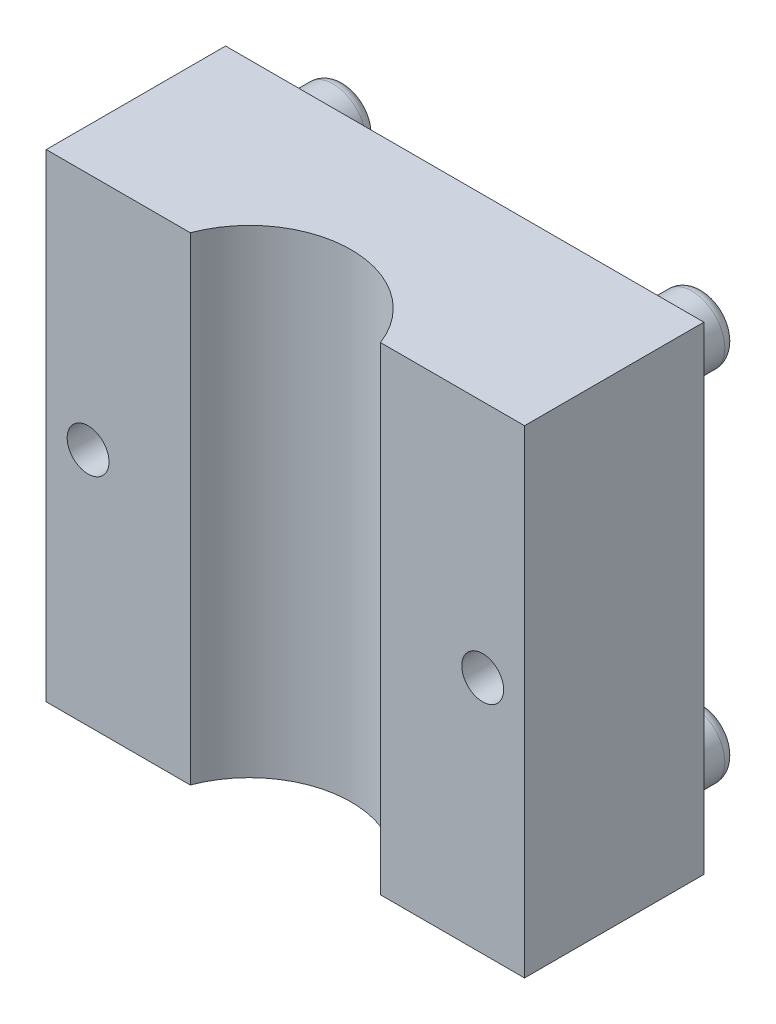
SolidWorks part; units mm, degrees
ref_plane "Front Plane" through (0, 0, 0) normal (0, 0, 1) x (1, 0, 0)
ref_plane "Top Plane" through (0, 0, 0) normal (0, 1, 0) x (1, 0, 0)
ref_plane "Right Plane" through (0, 0, 0) normal (1, 0, 0) x (0, 0, -1)
sketch "Sketch1" plane through (0, 0, 0) normal (0, 0, 1) x (1, 0, 0)
  line L1 (-20, 20) -> (20, 20)
  line L2 (-20, 20) -> (-20, -20)
  line L3 (-20, -20) -> (20, -20)
  line L4 (20, 20) -> (20, -20)
  line L5 (-20, 20) -> (20, -20) construction
  line L6 (-20, -20) -> (20, 20) construction
  point P0 (0, 0)
  dimension "D1" = 40
  dimension "D2" = 40
extrude "Boss-Extrude1" add sketch "Sketch1" along normal blind 15
sketch "Sketch3" plane through (0, 0, 0) normal (0, 0, -1) x (-1, 0, 0)
  line L0 (20, 20) -> (20, -20) construction
  line L1 (20, -20) -> (-20, -20) construction
  line L2 (-20, -20) -> (-20, 20) construction
  line L3 (-20, 20) -> (20, 20) construction
  circle A0 centre (-15, 15) radius 2.75
  circle A1 centre (15, 15) radius 2.75
  circle A2 centre (-15, -15) radius 2.75
  circle A3 centre (15, -15) radius 2.75
  dimension "D1" = 5.5
  dimension "D2" = 5.5
  dimension "D3" = 5.5
  dimension "D4" = 5.5
  dimension "D5" = 5
  dimension "D6" = 5
  dimension "D7" = 5
  dimension "D8" = 5
  dimension "D9" = 5
  dimension "D10" = 5
  dimension "D11" = 5
  dimension "D12" = 5
extrude "Boss-Extrude2" add sketch "Sketch3" along normal blind 5
fillet "Fillet1" radius 1 4 edges at (12.25, -15, -5) (-17.75, -15, -5) (-17.75, 15, -5) (12.25, 15, -5)
sketch "Sketch4" plane through (0, 0, 0) normal (0, 0, -1) x (-1, 0, 0)
  circle A0 centre (0, 0) radius 12.5
  dimension "D1" = 25
extrude "Cut-Extrude1" cut sketch "Sketch4" against normal blind 3.5
sketch "Sketch5" plane through (0, 20, 0) normal (0, 1, 0) x (1, 0, 0)
  line L0 (20, -15) -> (-20, -15) construction
  circle A0 centre (0, -18) radius 8.5
  point P2 (0, -15)
  dimension "D1" = 17
  dimension "D2" = 3
extrude "Cut-Extrude2" cut sketch "Sketch5" against normal through all
sketch "Sketch6" plane through (0, 0, 0) normal (0, 0, -1) x (-1, 0, 0)
  line L0 (-20, -20) -> (-20, 20) construction
  line L1 (20, 20) -> (20, -20) construction
  line L3 (-20, 20) -> (20, 20) construction
  circle A0 centre (-16.5, 0) radius 3
  circle A1 centre (16.5, 0) radius 3
  point P4 (-20, 0)
  point P11 (12.5513, 20)
  dimension "D1" = 6
  dimension "D2" = 6
  dimension "D3" = 3.5
  dimension "D4" = 3.5
  dimension "D5" = 20
  dimension "D6" = 20
extrude "Cut-Extrude3" cut sketch "Sketch6" against normal blind 2
sketch "Sketch7" plane through (0, 0, 0) normal (0, 0, -1) x (-1, 0, 0)
  circle A0 centre (16.5, 0) radius 1.75
  circle A1 centre (-16.5, 0) radius 1.75
  dimension "D1" = 3.5
  dimension "D2" = 3.5
extrude "Cut-Extrude4" cut sketch "Sketch7" against normal through all
